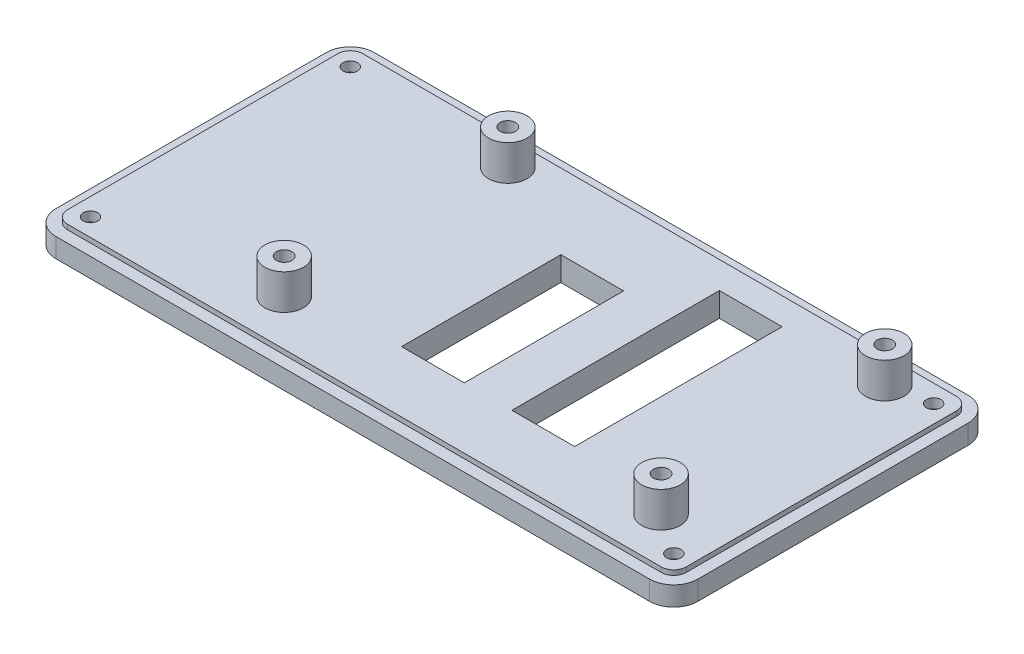
SolidWorks part; units mm, degrees
ref_plane "정면" through (0, 0, 0) normal (0, 0, 1) x (1, 0, 0)
ref_plane "윗면" through (0, 0, 0) normal (0, 1, 0) x (1, 0, 0)
ref_plane "우측면" through (0, 0, 0) normal (1, 0, 0) x (0, 0, -1)
sketch "스케치1" plane through (0, 0, 0) normal (0, 1, 0) x (1, 0, 0)
  line L0 (61.4984, 66.0105) -> (-61.5016, 65.9895)
  line L1 (-66.5008, 60.9895) -> (-66.5008, 4.9895)
  line L2 (-61.5, -0.0105) -> (61.5, 0.0105)
  line L3 (66.4992, 5.0105) -> (66.4992, 61.0105)
  arc A0 (-61.5016, 65.9895) -> (-66.5008, 60.9895) centre (-61.5008, 60.9895) ccw
  arc A1 (-66.5008, 4.9895) -> (-61.5, -0.0105) centre (-61.5008, 4.9895) ccw
  arc A2 (61.5, 0.0105) -> (66.4992, 5.0105) centre (61.4992, 5.0105) ccw
  arc A3 (66.4992, 61.0105) -> (61.4984, 66.0105) centre (61.4992, 61.0105) ccw
extrude "보스-돌출1" add sketch "스케치1" along normal blind 4
sketch "스케치2" plane through (0, 4, 0) normal (0, 1, 0) x (1, 0, 0)
  line L0 (61.4988, 63.6105) -> (-61.5012, 63.5895)
  line L1 (-64.1008, 60.9895) -> (-64.1008, 4.9895)
  line L2 (-61.5004, 2.3895) -> (61.4996, 2.4105)
  line L3 (64.0992, 5.0105) -> (64.0992, 61.0105)
  arc A0 (-61.5012, 63.5895) -> (-64.1008, 60.9895) centre (-61.5008, 60.9895) ccw
  arc A1 (-64.1008, 4.9895) -> (-61.5004, 2.3895) centre (-61.5008, 4.9895) ccw
  arc A2 (61.4996, 2.4105) -> (64.0992, 5.0105) centre (61.4992, 5.0105) ccw
  arc A3 (64.0992, 61.0105) -> (61.4988, 63.6105) centre (61.4992, 61.0105) ccw
extrude "보스-돌출2" add sketch "스케치2" along normal blind 1
sketch "스케치3" plane through (0, 5, 0) normal (0, 1, 0) x (1, 0, 0)
  line L0 (17.9407, 15.0385) -> (17.9407, 58.0385)
  line L1 (30.9407, 15.0385) -> (30.9407, 58.0385)
  line L2 (17.9407, 15.0385) -> (30.9407, 15.0385)
  line L3 (17.9407, 58.0385) -> (30.9407, 58.0385)
  line L4 (-4.9193, 15.0385) -> (-4.9193, 48.0385)
  line L5 (8.0807, 15.0385) -> (8.0807, 48.0385)
  line L6 (8.0807, 15.0385) -> (-4.9193, 15.0385)
  line L7 (8.0807, 48.0385) -> (-4.9193, 48.0385)
extrude "컷-돌출1" cut sketch "스케치3" against normal through all
sketch "스케치4" plane through (0, 5, 0) normal (0, 1, 0) x (1, 0, 0)
  circle A0 centre (-26.0424, 58.1763) radius 4
  circle A1 centre (52.0626, 58.1763) radius 4
  circle A2 centre (-26.0424, 11.8213) radius 4
  circle A3 centre (52.0626, 11.8213) radius 4
  circle A4 centre (52.0626, 58.1763) radius 1.6
  circle A5 centre (52.0626, 11.8213) radius 1.6
  circle A6 centre (-26.0424, 58.1763) radius 1.6
  circle A7 centre (-26.0424, 11.8213) radius 1.6
extrude "보스-돌출4" add sketch "스케치4" along normal blind 7.3
sketch "스케치5" plane through (0, 5, 0) normal (0, 1, 0) x (1, 0, 0)
  circle A0 centre (60.4401, 59.9288) radius 1.5
  circle A1 centre (60.4401, 6.0921) radius 1.5
  circle A2 centre (-60.4427, 59.9288) radius 1.5
  circle A3 centre (-60.4427, 6.0921) radius 1.5
extrude "컷-돌출2" cut sketch "스케치5" against normal blind 7.3
sketch "스케치6" plane through (0, 0, 0) normal (0, -1, 0) x (1, 0, 0)
  circle A0 centre (60.4504, -59.9185) radius 3.5
  circle A1 centre (60.4412, -6.0818) radius 3.5
  circle A2 centre (-60.4325, -59.9391) radius 3.5
  circle A3 centre (-60.4417, -6.1024) radius 3.5
extrude "컷-돌출3" cut sketch "스케치6" against normal blind 3
